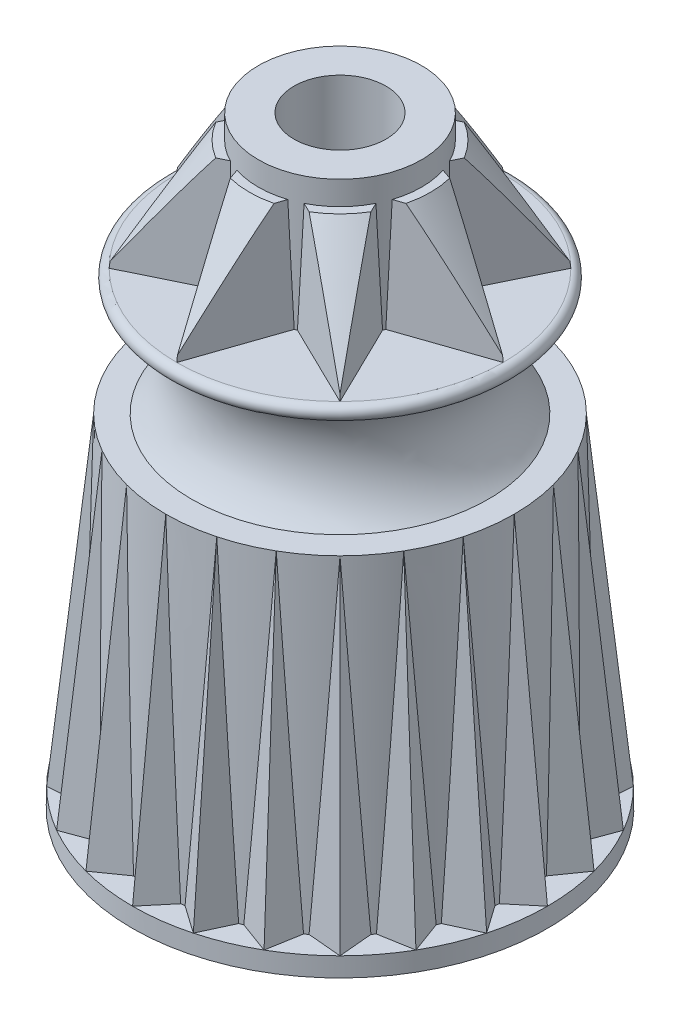
SolidWorks part; units mm, degrees
material "CA"
ref_plane "Front Plane" through (0, 0, 0) normal (0, 0, 1) x (1, 0, 0)
ref_plane "Top Plane" through (0, 0, 0) normal (0, 1, 0) x (1, 0, 0)
ref_plane "Right Plane" through (0, 0, 0) normal (1, 0, 0) x (0, 0, -1)
sketch "Sketch1" plane through (0, 0, 0) normal (0, 1, 0) x (1, 0, 0)
  circle A0 centre (0, 0) radius 8.89
  dimension "D1" = 17.78
extrude "Boss-Extrude1" add sketch "Sketch1" along normal blind 0.8128 draft 1
ref_plane "Plane1" through (0, 14.6304, 0) normal (0, 1, 0) x (1, 0, 0)
sketch "Sketch2" plane through (0, 14.6304, 0) normal (0, 1, 0) x (1, 0, 0)
  circle A0 centre (0, 0) radius 7.4549
  dimension "D1" = 14.9098
sketch "Sketch3" plane through (0, 0.8128, 0) normal (0, 1, 0) x (1, 0, 0)
  circle A0 centre (0, 0) radius 7.8105
  dimension "D1" = 15.621
loft "Loft1" add profiles "Sketch2", "Sketch3"
sketch "Sketch4" plane through (0, 0, 0) normal (1, 0, 0) x (0, 0, -1)
  line L0 (-7.4549, 14.6304) -> (-7.8105, 0.8128) construction
  line L1 (-7.4549, 14.6304) -> (-7.8105, 0.8128) construction
  line L2 (-8.8758, 0.8128) -> (-8.89, 0) construction
  line L3 (-8.8758, 0.8128) -> (-8.89, 0) construction
  line L4 (-8.8758, 0.8128) -> (-7.4549, 14.6304)
ref_plane "Plane2" through (0, 0.8128, 8.8758) normal (0, 0.9948, -0.1023) x (1, 0, 0)
sketch "Sketch5" plane through (0, 0.8128, 8.8758) normal (0, 0.9948, -0.1023) x (1, 0, 0)
  line L0 (0, 0) -> (0, 2.0328) construction
  line L1 (0, 0) -> (0, 1.0597) construction
  line L2 (0, 0) -> (1.2788, 1.524)
  line L3 (0, 0) -> (-1.2788, 1.524)
  line L4 (1.2788, 1.524) -> (-1.2788, 1.524)
  ellipse E0 centre (0, 8.8293) end of major axis (-8.8758, 8.8293) minor radius 8.8293 construction
  dimension "D1" = 80
  dimension "D2" = 1.524
sweep "Sweep1" add profiles "Sketch5" path "Sketch4"
pattern_circular "CirPattern1" count 24 over 360 about axis through (0, 0, 0) along (0, 1, 0) of "Sweep1"
sketch "Sketch7" plane through (0, 0, 0) normal (1, 0, 0) x (0, 0, -1)
  line L0 (0, 0) -> (0, 25.5262) construction
  line L1 (0, 0.8128) -> (0, 14.6304) construction
  line L2 (0, 20.0152) -> (6.985, 20.0152)
  line L3 (6.985, 19.3802) -> (6.35, 19.3802)
  line L4 (1.9295, 14.6304) -> (0, 14.6304) construction
  line L6 (16.7407, 14.6304) -> (0, 14.6304) construction
  line L7 (6.35, 14.6304) -> (0, 14.6304)
  line L8 (0, 14.6304) -> (0, 20.0152)
  arc A0 (6.985, 20.0152) -> (6.985, 19.3802) centre (6.985, 19.6977) cw
  arc A1 (6.35, 19.3802) -> (6.35, 14.6304) centre (8.6591, 17.0053) ccw
  dimension "D4" = 10.6934
  dimension "D1" = 12.7
  dimension "D2" = 0.635
  dimension "D3" = 0.635
  dimension "D5" = 4.7498
revolve "Revolve1" add sketch "Sketch7" angle 360 about L8
sketch "Sketch8" plane through (0, 20.0152, 0) normal (0, 1, 0) x (1, 0, 0)
  circle A0 centre (0, 0) radius 3.4925
  dimension "D1" = 6.985
extrude "Boss-Extrude2" add sketch "Sketch8" along a picked direction on the side of the normal offset from surface (5.7658 mm away) 25.781
sketch "Sketch9" plane through (0, 25.781, 0) normal (0, 1, 0) x (1, 0, 0)
  circle A0 centre (0, 0) radius 1.9685
  dimension "D1" = 3.937
extrude "Cut-Extrude1" cut sketch "Sketch9" against normal through all
sketch "Sketch10" plane through (0, 20.0152, 0) normal (0, 1, 0) x (1, 0, 0)
  line L0 (0, 0) -> (0, -9.673) construction
  line L1 (0, -6.985) -> (-1.5664, -2.436)
  line L2 (0, -6.985) -> (1.5664, -2.436)
  line L3 (-1.5664, -2.436) -> (1.5664, -2.436)
  circle A0 centre (0, 0) radius 6.985 construction
  dimension "D1" = 4.549
  dimension "D2" = 38
extrude "Boss-Extrude3" add sketch "Sketch10" along normal offset from surface 1.016 draft 2
pattern_circular "CirPattern2" count 8 over 360 about axis through (0, 0, 0) along (0, 1, 0) of "Boss-Extrude3"
sketch "Sketch11" plane through (0, 0, 0) normal (1, 0, 0) x (0, 0, -1)
  line L0 (3.4925, 24.765) -> (3.4925, 25.781) construction
  line L1 (3.4925, 24.765) -> (3.4925, 25.781)
  line L2 (6.4755, 24.765) -> (6.985, 20.0152) construction
  line L3 (6.4755, 24.765) -> (6.985, 20.0152) construction
  line L4 (3.4925, 24.765) -> (6.9579, 20.2678) construction
  line L5 (6.9579, 20.2678) -> (7.4659, 20.2678)
  line L6 (7.4659, 20.2678) -> (7.4659, 25.781)
  line L7 (7.4659, 25.781) -> (3.4925, 25.781)
  line L8 (3.4925, 24.765) -> (3.8735, 24.765)
  line L9 (1.5784, 24.765) -> (4.5789, 24.765) construction
  line L10 (3.8735, 24.765) -> (6.9579, 20.2678)
  dimension "D1" = 0.254
  dimension "D2" = 0.508
  dimension "D3" = 0.381
revolve "Cut-Revolve1" cut sketch "Sketch11" angle 360 about axis through (0, 61.4403, 0) along (0, -1, 0)
sketch "Sketch12" plane through (0, 0, 0) normal (1, 0, 0) x (0, 0, -1)
  line L0 (0, 0) -> (0, 28.1928) construction
  line L1 (2.921, 0) -> (3.1941, 15.6464)
  line L2 (3.1941, 15.6464) -> (4.5495, 15.6464)
  line L4 (-8.89, 0) -> (8.89, 0) construction
  line L5 (6.2319, 14.2909) -> (6.6263, 2.9972) construction
  line L6 (2.921, 0) -> (2.921, -2.54)
  line L7 (2.921, -2.54) -> (6.731, -2.54)
  line L8 (6.731, 0) -> (6.731, -2.54)
  line L9 (6.4484, 2.9972) -> (6.491, 1.778)
  line L10 (5.8897, 13.902) -> (6.2705, 2.9972)
  line L11 (6.491, 1.778) -> (6.6689, 1.778)
  line L12 (6.2705, 2.9972) -> (6.4484, 2.9972)
  line L13 (6.6689, 1.778) -> (6.731, 0)
  line L14 (6.0543, 14.2847) -> (6.5533, -0.0062) construction
  line L15 (5.8766, 14.2785) -> (6.3756, -0.0124) construction
  line L16 (5.6417, 13.902) -> (5.8897, 13.902)
  line L17 (6.2319, 14.2909) -> (6.731, 0) construction
  circle A0 centre (0, 0) radius 2.921 construction
  arc A1 (6.35, 19.3802) -> (6.35, 14.6304) centre (8.6591, 17.0053) ccw construction
  arc A2 (6.35, 19.3802) -> (6.35, 14.6304) centre (8.6591, 17.0053) ccw construction
  arc A3 (4.5495, 15.6464) -> (5.6417, 13.902) centre (8.6591, 17.0053) ccw
  circle A4 centre (0, 0) radius 6.731 construction
  arc A5 (5.6417, 20.1086) -> (5.6417, 13.902) centre (8.6591, 17.0053) ccw construction
  dimension "D1" = 5.842
  dimension "D6" = 13.462
  dimension "D3" = 1
  dimension "D4" = 15.6464
  dimension "D5" = 2
  dimension "D7" = 2.54
  dimension "D10" = 1.778
  dimension "D11" = 2.9972
  dimension "D2" = 1.016
  dimension "D8" = 0.1778
  dimension "D9" = 0.1778
revolve "Cut-Revolve2" cut sketch "Sketch12" angle 360 about L0
fillet "Fillet1" radius 0.762 1 edges at (0, 0, -6.731)
sketch "Sketch13" plane through (0, 1.778, 0) normal (0, -1, 0) x (1, 0, 0)
  line L0 (0, -6.491) -> (0, -2.4467)
  line L1 (0, 2.4467) -> (0, 6.491)
  circle A0 centre (0, 0) radius 6.491 construction
  circle A1 centre (0, 0) radius 2.4467 construction
rib "Rib1" sketch "Sketch13" sketch "Sketch13" thickness 1.016 parameters "D1"=1.016, "D3"=1
fillet "Fillet2" radius 0.508 8 edges at (0.508, 1.778, 4.6895) (-0.6093, 7.5791, 2.9919) (-0.508, 1.778, 4.6895) (0.6093, 7.5791, 2.9919) (-0.508, 1.778, -4.6895) (0.508, 1.778, -4.6895)
ref_plane "Plane3" through (0, 17.145, 0) normal (0, 1, 0) x (1, 0, 0)
sketch "Sketch14" plane through (0, 17.145, 0) normal (0, 1, 0) x (1, 0, 0)
  circle A0 centre (0, 0) radius 7.9375 construction
  dimension "D1" = 15.875
